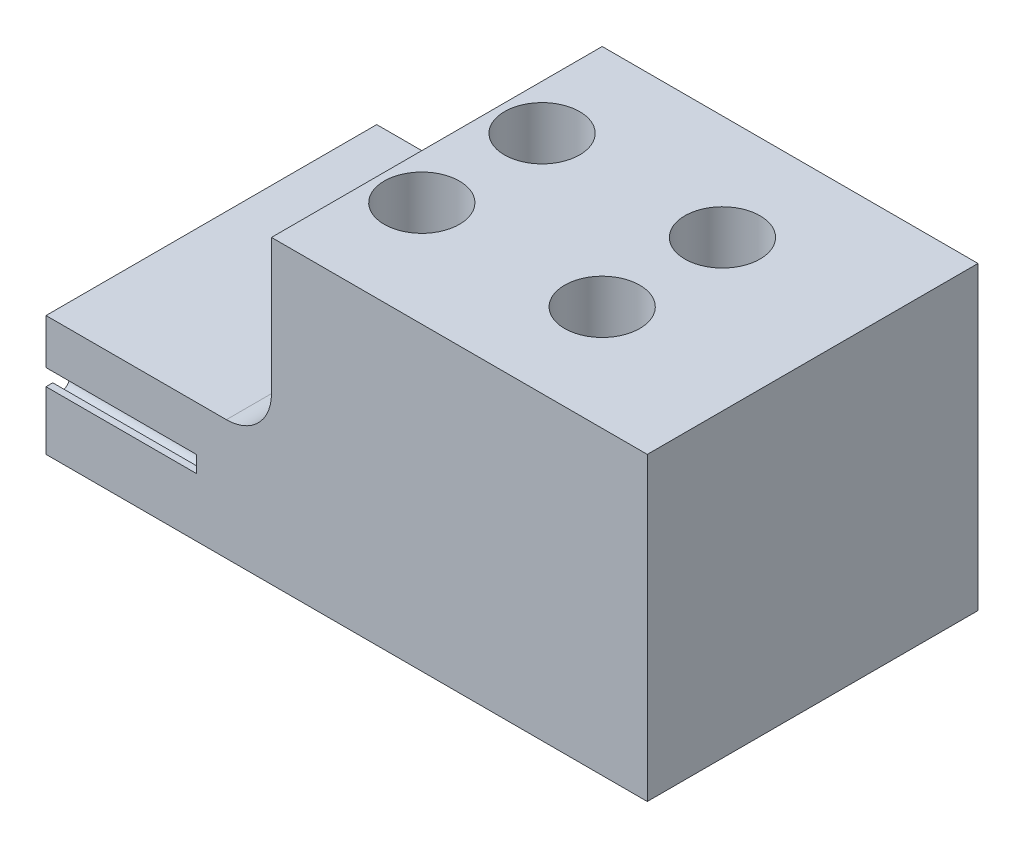
SolidWorks part; units mm, degrees
ref_plane "前视基准面" through (0, 0, 0) normal (0, 0, 1) x (1, 0, 0)
ref_plane "上视基准面" through (0, 0, 0) normal (0, 1, 0) x (1, 0, 0)
ref_plane "右视基准面" through (0, 0, 0) normal (1, 0, 0) x (0, 0, -1)
sketch "草图1" plane through (0, 0, 0) normal (0, 0, 1) x (1, 0, 0)
  line L1 (0, 0) -> (20, 0)
  line L2 (0, 0) -> (0, 30)
  line L3 (0, 30) -> (20, 30)
  line L4 (20, 0) -> (20, 30)
  dimension "D1" = 20
  dimension "D2" = 30
extrude "凸台-拉伸1" add sketch "草图1" along normal blind 30
sketch "草图3" plane through (0, 0, 0) normal (-1, 0, 0) x (0, 0, 1)
  line L0 (15, 0) -> (15, 30) construction
  line L1 (30, 30) -> (30, 0) construction
  line L2 (15, 3.1) -> (13, 3.1) construction
  line L4 (0, 30) -> (0, 0) construction
  line L6 (11.55, 3.65) -> (11.55, 3.8998)
  line L8 (12.45, 3.8998) -> (11.55, 3.8998)
  line L9 (12.45, 3.6498) -> (12.45, 3.8998)
  line L13 (11, 22.0922) -> (11, 23.6062) construction
  line L46 (13, 22.0922) -> (13, 23.9598) construction
  line L47 (9, 22.0922) -> (9, 23.9598) construction
  line L48 (7, 23) -> (9, 23) construction
  line L49 (7.55, 3.65) -> (7.55, 3.8998)
  line L50 (8.45, 3.8998) -> (7.55, 3.8998)
  line L51 (13.55, 3.6498) -> (13.55, 3.8998)
  line L52 (13.55, 3.8998) -> (14.45, 3.8998)
  line L53 (14.45, 3.65) -> (14.45, 3.8998)
  line L87 (8.45, 3.6498) -> (8.45, 3.8998)
  line L88 (9.55, 3.6498) -> (9.55, 3.8998)
  line L89 (9.55, 3.8998) -> (10.45, 3.8998)
  line L91 (10.45, 3.65) -> (10.45, 3.8998)
  line L92 (7, 22.0922) -> (7, 24.2983) construction
  line L93 (3.55, 3.65) -> (3.55, 3.8998)
  line L94 (4.45, 3.8998) -> (3.55, 3.8998)
  line L95 (4.45, 3.6498) -> (4.45, 3.8998)
  line L96 (5.55, 3.6498) -> (5.55, 3.8998)
  line L97 (-0.45, 3.65) -> (-0.45, 3.8998)
  line L98 (0.45, 3.8998) -> (-0.45, 3.8998)
  line L99 (0.45, 3.6498) -> (0.45, 3.8998)
  line L100 (5.55, 3.8998) -> (6.45, 3.8998)
  line L101 (6.45, 3.65) -> (6.45, 3.8998)
  line L102 (1.55, 3.6498) -> (1.55, 3.8998)
  line L103 (1.55, 3.8998) -> (2.45, 3.8998)
  line L104 (2.45, 3.65) -> (2.45, 3.8998)
  line L105 (-1, 3.1) -> (-1, 5)
  line L106 (-1, 5) -> (15, 5)
  line L107 (23, 22.0922) -> (23, 24.2983) construction
  line L108 (23, 23) -> (21, 23) construction
  line L109 (21, 22.0922) -> (21, 23.9598) construction
  line L110 (17, 22.0922) -> (17, 23.9598) construction
  line L111 (19, 22.0922) -> (19, 23.6062) construction
  line L112 (15, 3.1) -> (17, 3.1) construction
  line L113 (27.55, 3.65) -> (27.55, 3.8998)
  line L114 (28.45, 3.8998) -> (27.55, 3.8998)
  line L115 (28.45, 3.6498) -> (28.45, 3.8998)
  line L116 (23.55, 3.65) -> (23.55, 3.8998)
  line L117 (24.45, 3.8998) -> (23.55, 3.8998)
  line L118 (29.55, 3.6498) -> (29.55, 3.8998)
  line L119 (29.55, 3.8998) -> (30.45, 3.8998)
  line L120 (30.45, 3.65) -> (30.45, 3.8998)
  line L121 (24.45, 3.6498) -> (24.45, 3.8998)
  line L122 (25.55, 3.6498) -> (25.55, 3.8998)
  line L123 (25.55, 3.8998) -> (26.45, 3.8998)
  line L124 (26.45, 3.65) -> (26.45, 3.8998)
  line L125 (19.55, 3.65) -> (19.55, 3.8998)
  line L126 (20.45, 3.8998) -> (19.55, 3.8998)
  line L127 (20.45, 3.6498) -> (20.45, 3.8998)
  line L128 (21.55, 3.6498) -> (21.55, 3.8998)
  line L129 (15.55, 3.65) -> (15.55, 3.8998)
  line L130 (16.45, 3.8998) -> (15.55, 3.8998)
  line L131 (16.45, 3.6498) -> (16.45, 3.8998)
  line L132 (21.55, 3.8998) -> (22.45, 3.8998)
  line L133 (22.45, 3.65) -> (22.45, 3.8998)
  line L134 (17.55, 3.6498) -> (17.55, 3.8998)
  line L135 (17.55, 3.8998) -> (18.45, 3.8998)
  line L136 (18.45, 3.65) -> (18.45, 3.8998)
  line L137 (15, 5) -> (31, 5)
  line L138 (31, 5) -> (31, 3.1)
  line L139 (30, 30) -> (0, 30) construction
  arc A17 (15.55, 3.65) -> (14.45, 3.65) centre (15, 3.65) cw
  arc A24 (13.55, 3.6498) -> (12.45, 3.6498) centre (13, 3.65) cw
  arc A26 (10.45, 3.65) -> (11.55, 3.65) centre (11, 3.65) ccw
  arc A28 (8.45, 3.6498) -> (9.55, 3.6498) centre (9, 3.65) ccw
  arc A29 (6.45, 3.65) -> (7.55, 3.65) centre (7, 3.65) ccw
  arc A30 (-1, 3.1) -> (-0.45, 3.65) centre (-1, 3.65) ccw
  arc A31 (5.55, 3.6498) -> (4.45, 3.6498) centre (5, 3.65) cw
  arc A32 (3.55, 3.65) -> (2.45, 3.65) centre (3, 3.65) cw
  arc A33 (0.45, 3.6498) -> (1.55, 3.6498) centre (1, 3.65) ccw
  arc A34 (29.55, 3.6498) -> (28.45, 3.6498) centre (29, 3.65) cw
  arc A35 (26.45, 3.65) -> (27.55, 3.65) centre (27, 3.65) ccw
  arc A36 (24.45, 3.6498) -> (25.55, 3.6498) centre (25, 3.65) ccw
  arc A37 (31, 3.1) -> (30.45, 3.65) centre (31, 3.65) cw
  arc A38 (23.55, 3.65) -> (22.45, 3.65) centre (23, 3.65) cw
  arc A39 (21.55, 3.6498) -> (20.45, 3.6498) centre (21, 3.65) cw
  arc A40 (19.55, 3.65) -> (18.45, 3.65) centre (19, 3.65) cw
  arc A41 (16.45, 3.6498) -> (17.55, 3.6498) centre (17, 3.65) ccw
  dimension "D1" = 0.9
  dimension "D3" = 0.55
  dimension "D5" = 25
  dimension "D4" = 0.55
  dimension "D2" = 0.25
  dimension "D6" = 1.9
  dimension "D7" = 2
extrude "切除-拉伸1" cut sketch "草图3" against normal blind 10
sketch "草图15" plane through (0, 30, 0) normal (0, 1, 0) x (1, 0, 0)
  line L4 (20, 0) -> (0, 0)
  line L5 (0, 0) -> (0, -30)
  line L6 (0, -30) -> (20, -30)
  line L7 (20, -30) -> (20, 0)
  line L8 (20, 0) -> (0, 0)
  line L9 (0, 0) -> (0, -30)
  line L10 (0, -30) -> (20, -30)
  line L11 (20, -30) -> (20, 0)
  dimension "D1" = 0
extrude "切除-拉伸6" cut sketch "草图15" against normal blind 10
sketch "草图16" plane through (20, 0, 0) normal (1, 0, 0) x (0, 0, -1)
  line L4 (0, 20) -> (-30, 20)
  line L5 (-30, 20) -> (-30, 0)
  line L6 (-30, 0) -> (0, 0)
  line L7 (0, 0) -> (0, 20)
  line L8 (0, 20) -> (-30, 20)
  line L9 (-30, 20) -> (-30, 0)
  line L10 (-30, 0) -> (0, 0)
  line L11 (0, 0) -> (0, 20)
  dimension "D1" = 0
extrude "凸台-拉伸5" add sketch "草图16" along normal blind 20
hole_wizard "M2 间隙孔2" positions "草图18" profile "草图19" hole size "M2" standard "ISO" end condition through all
sketch "草图18" plane through (0, 20, 0) normal (0, 1, 0) x (1, 0, 0)
  line L0 (41.773, -15) -> (25.5653, -15) construction
  line L1 (40, 0) -> (40, -30) construction
  point P7 (18, -11)
  point P9 (30, -11)
  point P20 (30, -19)
  point P21 (18, -19)
  dimension "D1" = 4
  dimension "D2" = 4
  dimension "D3" = 10
  dimension "D4" = 12
sketch "草图19" plane through (18, 20, 19) normal (1, 0, 0) x (0, 0, 1)
  line L0 (0, 0) -> (0, 20)
  line L1 (0, 20) -> (1.2, 20)
  line L2 (1.2, 20) -> (1.2, 0.025)
  line L3 (1.2, 0.025) -> (1.225, 0)
  line L5 (1.225, 0) -> (0, 0)
  line L6 (-1.2, 0.025) -> (-1.225, 0) construction
  line L11 (0, -6.35) -> (0, 107.95) construction
  dimension "通孔孔直径" = 2.4
  dimension "通孔孔深度" = 20
  dimension "近端锥形沉头孔直径" = 2.45
  dimension "近端锥形沉头孔角度" = 90
sketch "草图20" plane through (0, 20, 0) normal (0, 1, 0) x (1, 0, 0)
  circle A0 centre (18, -11) radius 2.5
  circle A1 centre (30, -11) radius 2.5
  circle A2 centre (30, -19) radius 2.5
  circle A3 centre (18, -19) radius 2.5
  dimension "D1" = 5
  dimension "D2" = 5
  dimension "D3" = 5
  dimension "D4" = 5
extrude "切除-拉伸7" cut sketch "草图20" against normal blind 12
sketch "草图21" plane through (0, 0, 0) normal (0, 0, -1) x (-1, 0, 0)
  line L1 (0, 20) -> (-15, 20)
  line L2 (0, 20) -> (0, 8)
  line L3 (0, 8) -> (-15, 8)
  line L4 (-15, 20) -> (-15, 8)
  dimension "D1" = 15
  dimension "D2" = 12
extrude "切除-拉伸8" cut sketch "草图21" against normal through all
sketch "草图22" plane through (0, 0, 0) normal (0, -1, 0) x (1, 0, 0)
  line L0 (40, 30) -> (40, 0) construction
  line L1 (0, 30) -> (40, 30)
  line L2 (0, 30) -> (0, 26)
  line L3 (0, 26) -> (40, 26)
  line L4 (40, 30) -> (40, 26)
  line L6 (0, 0) -> (40, 0)
  line L7 (0, 0) -> (0, 4)
  line L8 (0, 4) -> (40, 4)
  line L9 (40, 0) -> (40, 4)
  dimension "D1" = 4
  dimension "D2" = 4
extrude "切除-拉伸9" cut sketch "草图22" against normal through all
fillet "圆角1" radius 3 1 edges at (15, 8, 15)
